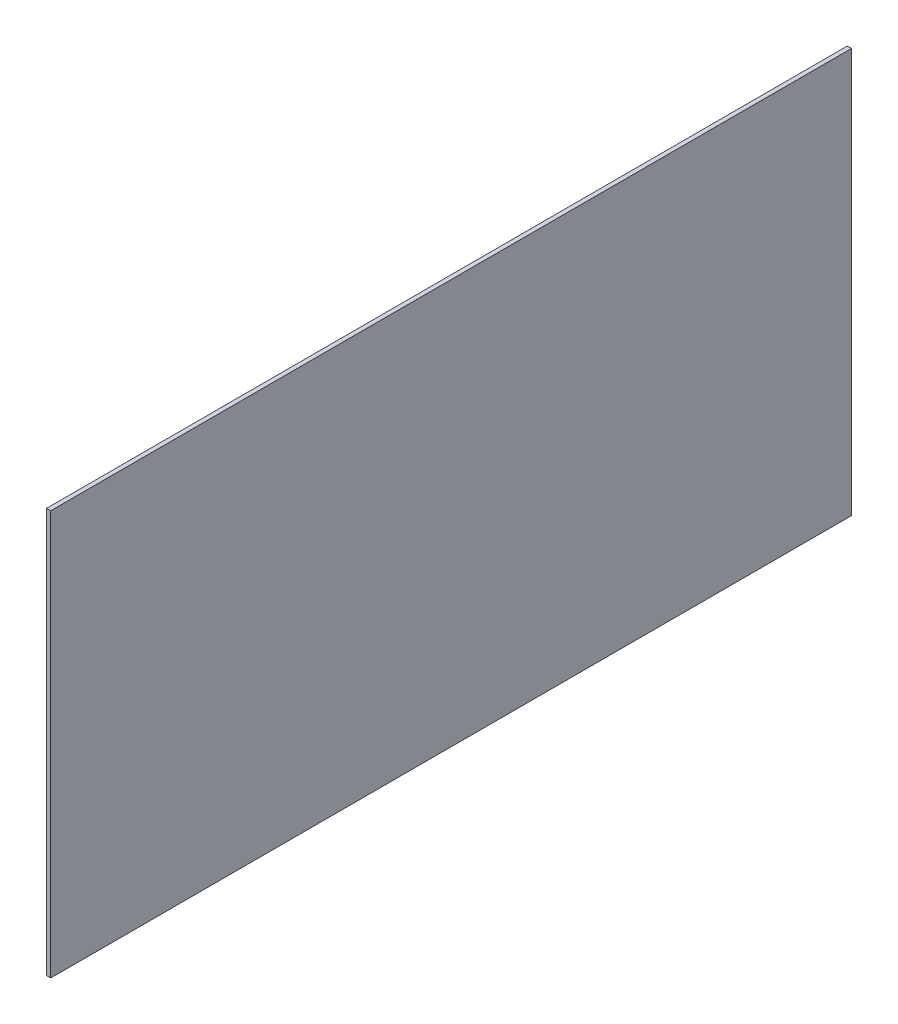
SolidWorks part; units mm, degrees
ref_plane "Front Plane" through (0, 0, 0) normal (0, 0, 1) x (1, 0, 0)
ref_plane "Top Plane" through (0, 0, 0) normal (0, 1, 0) x (1, 0, 0)
ref_plane "Right Plane" through (0, 0, 0) normal (1, 0, 0) x (0, 0, -1)
sketch "Sketch1" plane through (0, 0, 0) normal (1, 0, 0) x (0, 0, -1)
  line L1 (304.8, -152.4) -> (-304.8, -152.4)
  line L2 (304.8, -152.4) -> (304.8, 152.4)
  line L3 (304.8, 152.4) -> (-304.8, 152.4)
  line L4 (-304.8, -152.4) -> (-304.8, 152.4)
  line L5 (304.8, -152.4) -> (-304.8, 152.4) construction
  line L6 (304.8, 152.4) -> (-304.8, -152.4) construction
  point P0 (0, 0)
  dimension "D1" = 609.6
  dimension "D2" = 304.8
extrude "Boss-Extrude1" add sketch "Sketch1" along normal blind 3.175 contours L3 L4 L1 L2
sketch "Sketch2" plane through (0, 0, -304.8) normal (0, 0, -1) x (-1, 0, 0)
  line L1 (-3.175, 152.4) -> (0, 152.4)
  line L2 (-3.175, 152.4) -> (-3.175, -152.4)
  line L3 (-3.175, -152.4) -> (0, -152.4)
  line L4 (0, 152.4) -> (0, -152.4)
extrude "Cut-Extrude1" cut sketch "Sketch2" against normal blind 6.35
